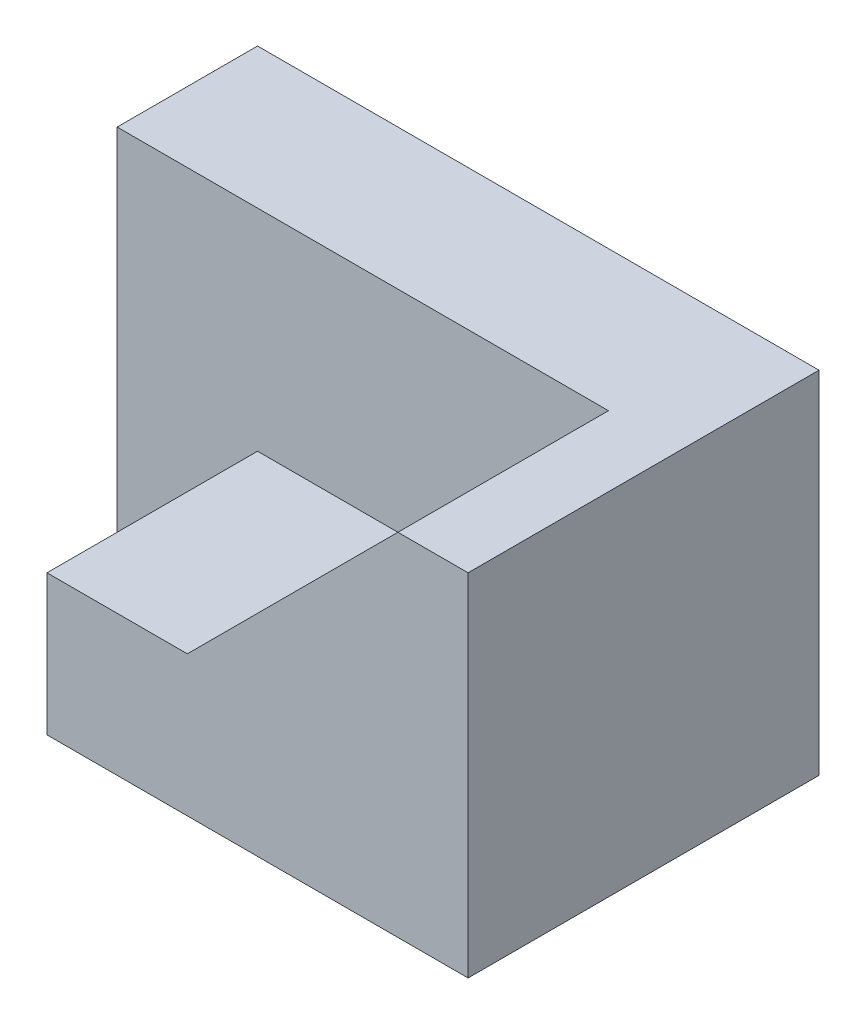
SolidWorks part; units mm, degrees
ref_plane "Front Plane" through (0, 0, 0) normal (0, 0, 1) x (1, 0, 0)
ref_plane "Top Plane" through (0, 0, 0) normal (0, 1, 0) x (1, 0, 0)
ref_plane "Right Plane" through (0, 0, 0) normal (1, 0, 0) x (0, 0, -1)
sketch "Sketch1" plane through (0, 0, 0) normal (0, 0, 1) x (1, 0, 0)
  line L1 (0, 0) -> (80, 0)
  line L2 (0, 0) -> (0, 50)
  line L3 (0, 50) -> (80, 50)
  line L4 (80, 0) -> (80, 50)
  dimension "D1" = 80
  dimension "D2" = 50
extrude "Boss-Extrude1" add sketch "Sketch1" along normal blind 50
sketch "Sketch2" plane through (0, 0, 50) normal (0, 0, 1) x (1, 0, 0)
  line L0 (20, 0) -> (0, 0)
  line L1 (0, 0) -> (80, 0) construction
  line L2 (0, 0) -> (0, 50)
  line L3 (0, 50) -> (70, 50)
  line L4 (80, 50) -> (0, 50) construction
  line L5 (70, 50) -> (40, 20)
  line L6 (40, 20) -> (20, 20)
  line L7 (20, 20) -> (20, 0)
  dimension "D1" = 20
  dimension "D2" = 20
  dimension "D3" = 20
  dimension "D4" = 10
extrude "Cut-Extrude1" cut sketch "Sketch2" against normal blind 30
